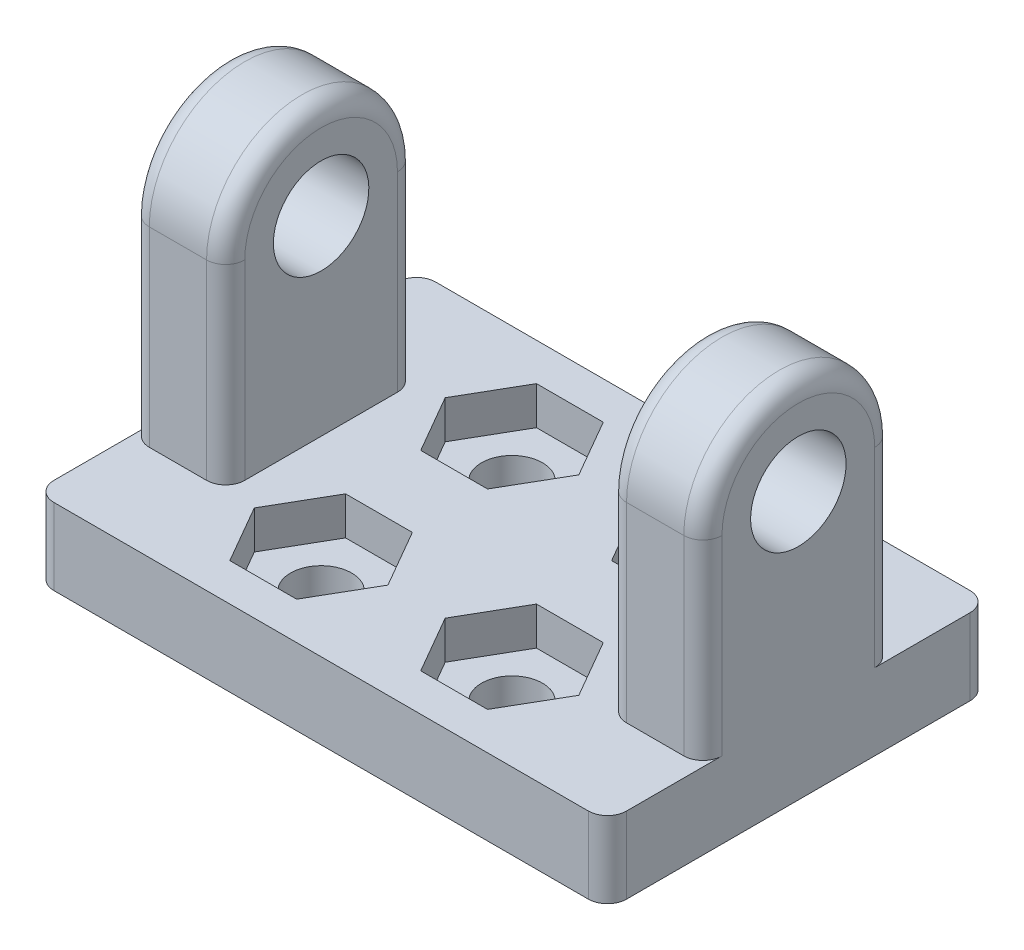
SolidWorks part; units mm, degrees
ref_plane "Plan de face" through (0, 0, 0) normal (0, 0, 1) x (1, 0, 0)
ref_plane "Plan de dessus" through (0, 0, 0) normal (0, 1, 0) x (1, 0, 0)
ref_plane "Plan de droite" through (0, 0, 0) normal (1, 0, 0) x (0, 0, -1)
sketch "Esquisse2" plane through (0, 0, 0) normal (1, 0, 0) x (0, 0, -1)
  line L0 (5, 0) -> (5, -10)
  line L2 (-5, 0) -> (-5, -10)
  line L3 (-5, -10) -> (5, -10)
  circle A0 centre (0, 0) radius 2.5
  arc A2 (5, 0) -> (-5, 0) centre (0, 0) ccw
  dimension "D1" = 5
  dimension "D2" = 10
  dimension "D3" = 5
  dimension "D4" = 5
extrude "Boss.-Extru.1" add sketch "Esquisse2" along normal mid plane 30
sketch "Esquisse4" plane through (0, -10, 0) normal (0, -1, 0) x (1, 0, 0)
  line L0 (-15, 5) -> (-15, -5) construction
  line L1 (-15, -10) -> (15, -10)
  line L2 (-15, -10) -> (-15, 10)
  line L3 (-15, 10) -> (15, 10)
  line L4 (15, -10) -> (15, 10)
  line L5 (15, 5) -> (15, -5) construction
  dimension "D1" = 20
  dimension "D4" = 10
extrude "Boss.-Extru.2" add sketch "Esquisse4" along normal blind 4
sketch "Esquisse5" plane through (0, -10, 0) normal (0, 1, 0) x (1, 0, 0)
  circle A0 centre (5, -5) radius 1.6
  circle A1 centre (5, 5) radius 1.6
  circle A2 centre (-5, 5) radius 1.6
  circle A3 centre (-5, -5) radius 1.6
  point P15 (0, 0)
  dimension "D1" = 3.2
  dimension "D2" = 10
  dimension "D3" = 10
  dimension "D4" = 5
  dimension "D5" = 5
extrude "Enlèv. mat.-Extru.1" cut sketch "Esquisse5" against normal up to next contours A0
sketch "Esquisse6" plane through (0, 0, 5) normal (0, 0, 1) x (1, 0, 0)
  line L0 (15, -10) -> (6.6, -10) construction
  line L1 (-10, 11.5437) -> (10, 11.5437)
  line L2 (-10, 11.5437) -> (-10, -10)
  line L3 (-10, -10) -> (10, -10)
  line L4 (10, 11.5437) -> (10, -10)
  line L5 (15, 0) -> (-15, 0) construction
  point P7 (0, 11.5437)
  point P11 (0, 0)
  dimension "D2" = 20
extrude "Enlèv. mat.-Extru.2" cut sketch "Esquisse6" against normal through all
sketch "Esquisse7" plane through (0, -10, 0) normal (0, 1, 0) x (1, 0, 0)
  line L8 (-1.5, -5) -> (-3.25, -1.9689)
  line L9 (-3.25, -1.9689) -> (-6.75, -1.9689)
  line L10 (-6.75, -1.9689) -> (-8.5, -5)
  line L11 (-8.5, -5) -> (-6.75, -8.0311)
  line L12 (-6.75, -8.0311) -> (-3.25, -8.0311)
  line L13 (-3.25, -8.0311) -> (-1.5, -5)
  line L14 (8.5, -5) -> (6.75, -1.9689)
  line L15 (6.75, -1.9689) -> (3.25, -1.9689)
  line L16 (3.25, -1.9689) -> (1.5, -5)
  line L17 (1.5, -5) -> (3.25, -8.0311)
  line L18 (3.25, -8.0311) -> (6.75, -8.0311)
  line L19 (6.75, -8.0311) -> (8.5, -5)
  line L20 (8.5, 5) -> (6.75, 8.0311)
  line L21 (6.75, 8.0311) -> (3.25, 8.0311)
  line L22 (3.25, 8.0311) -> (1.5, 5)
  line L23 (1.5, 5) -> (3.25, 1.9689)
  line L24 (3.25, 1.9689) -> (6.75, 1.9689)
  line L25 (6.75, 1.9689) -> (8.5, 5)
  line L26 (-1.5, 5) -> (-3.25, 8.0311)
  line L27 (-3.25, 8.0311) -> (-6.75, 8.0311)
  line L28 (-6.75, 8.0311) -> (-8.5, 5)
  line L29 (-8.5, 5) -> (-6.75, 1.9689)
  line L30 (-6.75, 1.9689) -> (-3.25, 1.9689)
  line L31 (-3.25, 1.9689) -> (-1.5, 5)
  line L32 (-15, 10) -> (15, 10) construction
  line L33 (15, -10) -> (-15, -10) construction
  circle A5 centre (-5, -5) radius 3.0311 construction
  circle A6 centre (5, -5) radius 3.0311 construction
  circle A7 centre (5, 5) radius 3.0311 construction
  circle A8 centre (-5, 5) radius 3.0311 construction
  dimension "D1" = 3.5
  dimension "D2" = 3.5
  dimension "D3" = 3.5
  dimension "D4" = 3.5
extrude "Enlèv. mat.-Extru.3" cut sketch "Esquisse7" against normal blind 2 and the other way through all
fillet "Congé1" radius 1 16 edges at (10, -5, -5) (10, -5, 5) (-10, -5, 5) (-10, -5, -5) (15, -5, -5) (15, -5, 5) (-15, -5, -5) (-15, -5, 5) (10, 5, 0) (-10, 5, 0) (15, 5, 0) (-15, 5, 0) (-15, -12, -10) (-15, -12, 10) (15, -12, -10) (15, -12, 10)
